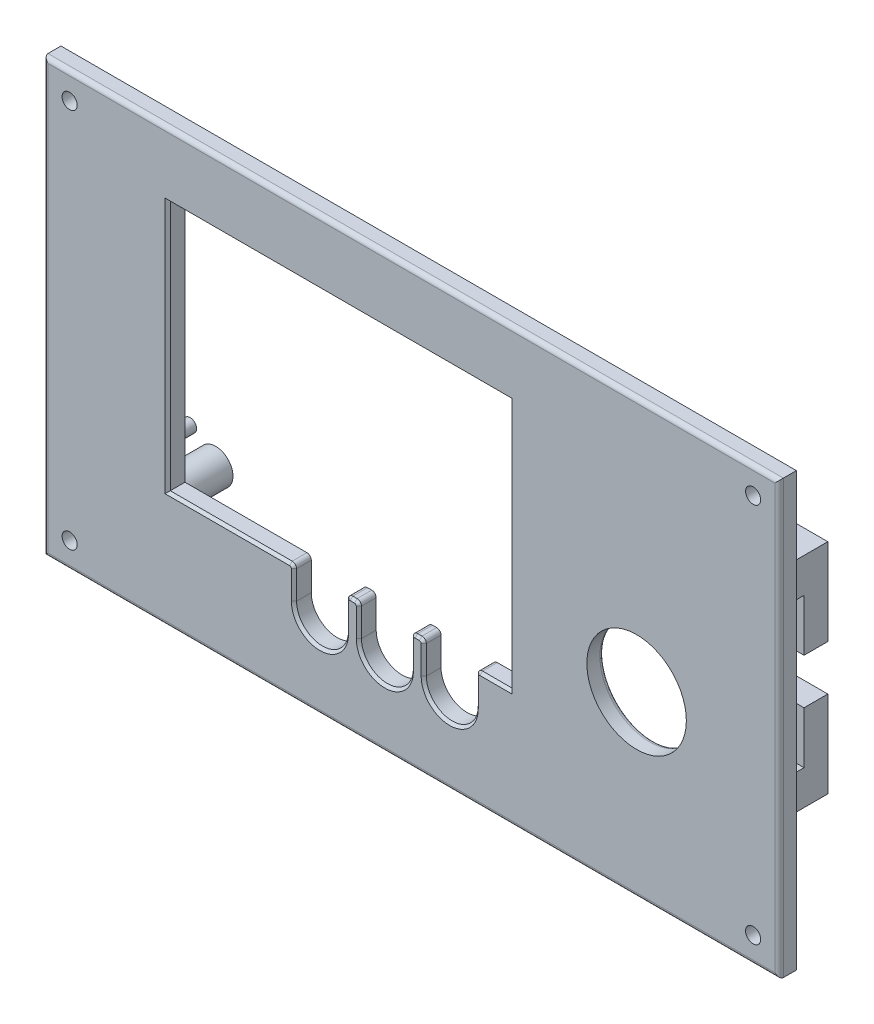
SolidWorks part; units mm, degrees
ref_plane "前视基准面" through (0, 0, 0) normal (0, 0, 1) x (1, 0, 0)
ref_plane "上视基准面" through (0, 0, 0) normal (0, 1, 0) x (1, 0, 0)
ref_plane "右视基准面" through (0, 0, 0) normal (1, 0, 0) x (0, 0, -1)
sketch "草图1" plane through (0, 0, 0) normal (0, 0, 1) x (1, 0, 0)
  line L0 (-37.3122, -36.0521) -> (-37.3122, -29.5521)
  line L1 (-95.1737, 44.4479) -> (74.8263, 44.4479)
  line L2 (-95.1737, 44.4479) -> (-95.1737, -55.5521)
  line L3 (-95.1737, -55.5521) -> (74.8263, -55.5521)
  line L4 (74.8263, 44.4479) -> (74.8263, -55.5521)
  line L5 (-66.5122, 29.4479) -> (12.4878, 29.4479)
  line L6 (-66.5122, 29.4479) -> (-66.5122, -28.5521)
  line L7 (-66.5122, -28.5521) -> (-38.3122, -28.5521)
  line L8 (12.4878, 29.4479) -> (12.4878, -28.5521)
  line L9 (-25.3122, -36.0521) -> (-25.3122, -29.5521)
  line L10 (-22.3122, -36.0521) -> (-22.3122, -29.5521)
  line L11 (-10.3122, -36.0521) -> (-10.3122, -29.5521)
  line L12 (4.6878, -36.0521) -> (4.6878, -29.5521)
  line L13 (-7.3122, -36.0521) -> (-7.3122, -29.5521)
  line L14 (-9.3122, -28.5521) -> (-8.3122, -28.5521)
  line L15 (-24.3122, -28.5521) -> (-23.3122, -28.5521)
  line L16 (5.6878, -28.5521) -> (12.4878, -28.5521)
  line L17 (-124.387, -5.5521) -> (115.7524, -5.5521) construction
  line L18 (-10.1737, 93.3642) -> (-10.1737, -86.2543) construction
  circle A0 centre (41.8878, -14.3521) radius 11.5
  arc A1 (-37.3122, -36.0521) -> (-25.3122, -36.0521) centre (-31.3122, -36.0521) ccw
  arc A2 (-22.3122, -36.0521) -> (-10.3122, -36.0521) centre (-16.3122, -36.0521) ccw
  arc A3 (-7.3122, -36.0521) -> (4.6878, -36.0521) centre (-1.3122, -36.0521) ccw
  arc A4 (4.6878, -29.5521) -> (5.6878, -28.5521) centre (5.6878, -29.5521) cw
  arc A5 (-7.3122, -29.5521) -> (-8.3122, -28.5521) centre (-8.3122, -29.5521) ccw
  arc A6 (-10.3122, -29.5521) -> (-9.3122, -28.5521) centre (-9.3122, -29.5521) cw
  arc A7 (-22.3122, -29.5521) -> (-23.3122, -28.5521) centre (-23.3122, -29.5521) ccw
  arc A8 (-25.3122, -29.5521) -> (-24.3122, -28.5521) centre (-24.3122, -29.5521) cw
  arc A9 (-37.3122, -29.5521) -> (-38.3122, -28.5521) centre (-38.3122, -29.5521) ccw
  circle A10 centre (-89.1737, 38.4479) radius 1.75
  circle A11 centre (68.8263, 38.4479) radius 1.75
  circle A12 centre (68.8263, -49.5521) radius 1.75
  circle A13 centre (-89.1737, -49.5521) radius 1.75
  point P15 (4.6878, -28.5521)
  point P30 (-7.3122, -28.5521)
  point P33 (-10.3122, -28.5521)
  point P38 (-25.3122, -28.5521)
  point P49 (0, 0)
  dimension "D7" = 23
  dimension "D9" = 12
  dimension "D10" = 15
  dimension "D11" = 15
  dimension "D12" = 13.8
  dimension "D13" = 7.5
  dimension "D14" = 1
  dimension "D15" = 3.5
  dimension "D16" = 6
  dimension "D1" = 170
  dimension "D2" = 100
  dimension "D3" = 58
  dimension "D4" = 79
  dimension "D5" = 29.4
  dimension "D6" = 14.2
  dimension "D8" = 15
  dimension "D17" = 6
extrude "凸台-拉伸1" add sketch "草图1" along normal blind 4
chamfer "倒角1" distance 0.6 angle 45 22 edges at (-37.6051, -28.845, 4) (-37.3122, -32.8021, 4) (-31.3122, -42.0521, 4) (-25.3122, -32.8021, 4) (-25.0193, -28.845, 4) (-23.8122, -28.5521, 4) (-22.6051, -28.845, 4) (-22.3122, -32.8021, 4) (-16.3122, -42.0521, 4) (-10.3122, -32.8021, 4) (-10.0193, -28.845, 4) (-8.8122, -28.5521, 4) (-7.6051, -28.845, 4) (-7.3122, -32.8021, 4) (-1.3122, -42.0521, 4) (4.6878, -32.8021, 4) (4.9807, -28.845, 4) (9.0878, -28.5521, 4) (-52.4122, -28.5521, 4) (12.4878, 0.4479, 4) (-27.0122, 29.4479, 4) (-66.5122, 0.4479, 4)
fillet "圆角1" radius 1 1 edges at (53.3878, -14.3521, 0)
sketch "草图2" plane through (0, 0, 0) normal (0, 0, -1) x (-1, 0, 0)
  line L0 (-66.1828, 0.4479) -> (115.6018, 0.4479) construction
  line L1 (-12.4878, 29.4479) -> (66.5122, 29.4479) construction
  line L2 (66.5122, -28.5521) -> (38.3122, -28.5521) construction
  line L3 (66.5122, 29.4479) -> (66.5122, -28.5521) construction
  line L4 (-17.9878, 25.3979) -> (73.3122, 25.3979) construction
  line L5 (-10.6878, -37.8021) -> (75.4122, -37.8021) construction
  circle A0 centre (-17.9878, 25.3979) radius 1.5
  circle A2 centre (73.3122, 25.3979) radius 1.5
  circle A3 centre (73.3122, -24.5021) radius 1.5
  circle A4 centre (-17.9878, -24.5021) radius 1.5
  circle A5 centre (75.4122, -37.8021) radius 4
  circle A6 centre (75.4122, -37.8021) radius 1.5
  circle A7 centre (-10.6878, -37.8021) radius 4
  arc A8 (-4.6878, -36.0521) -> (7.3122, -36.0521) centre (1.3122, -36.0521) ccw construction
  circle A9 centre (-10.6878, -37.8021) radius 1.5
  dimension "D1" = 91.3
  dimension "D2" = 6.8
  dimension "D3" = 3
  dimension "D4" = 13.3
  dimension "D5" = 2.1
  dimension "D6" = 8
  dimension "D7" = 3
  dimension "D8" = 12
  dimension "D9" = 8
  dimension "D10" = 3
  dimension "D11" = 49.9
extrude "凸台-拉伸2" add sketch "草图2" along normal blind 16
fillet "圆角2" radius 1 4 edges at (74.8263, -5.5521, 4) (-10.1737, 44.4479, 4) (-10.1737, -55.5521, 4) (-95.1737, -5.5521, 4)
sketch "草图3" plane through (0, 0, 0) normal (1, 0, 0) x (0, 0, -1)
  line L0 (0, -55.5521) -> (0, 44.4479) construction
  line L1 (8, 34.7762) -> (20.6651, 34.7762)
  line L2 (8, 34.7762) -> (8, -29.2158)
  line L3 (8, -29.2158) -> (20.6651, -29.2158)
  line L4 (20.6651, 34.7762) -> (20.6651, -29.2158)
  dimension "D1" = 8
extrude "切除-拉伸1" cut sketch "草图3" against normal mid plane 170
sketch "草图4" plane through (0, 0, 0) normal (0, 0, -1) x (-1, 0, 0)
  line L0 (-84.5714, -14.3521) -> (0, -14.3521) construction
  line L1 (-41.8878, 16.0764) -> (-41.8878, -50.4729) construction
  line L2 (-58.9378, -0.4521) -> (-58.9378, -26.4521) construction
  line L3 (-58.9378, -0.4521) -> (-24.8378, -0.4521) construction
  line L4 (-24.8378, -0.4521) -> (-24.8378, -26.4521) construction
  line L5 (-24.8378, -26.4521) -> (-58.9378, -26.4521) construction
  line L6 (-55.0878, -11.0719) -> (-55.0878, 15.8519) construction
  line L7 (-60.0878, 11.8479) -> (-50.0878, 11.8479)
  line L8 (-60.0878, 11.8479) -> (-60.0878, -8.1521)
  line L9 (-60.0878, -8.1521) -> (-50.0878, -8.1521)
  line L10 (-50.0878, 11.8479) -> (-50.0878, -8.1521)
  line L11 (-23.6878, -8.1521) -> (-33.6878, -8.1521)
  line L12 (-23.6878, 11.8479) -> (-33.6878, 11.8479)
  line L13 (-33.6878, 11.8479) -> (-33.6878, -8.1521)
  line L14 (-23.6878, 11.8479) -> (-23.6878, -8.1521)
  line L15 (-55.0878, -18.9352) -> (-55.0878, -43.9665) construction
  line L17 (-60.0878, -18.6521) -> (-50.0878, -18.6521)
  line L18 (-60.0878, -18.6521) -> (-60.0878, -38.6521)
  line L19 (-60.0878, -38.6521) -> (-50.0878, -38.6521)
  line L20 (-50.0878, -18.6521) -> (-50.0878, -38.6521)
  circle A0 centre (-28.6878, -3.1521) radius 1.5 construction
  circle A1 centre (-55.0878, -3.1521) radius 1.5 construction
  circle A2 centre (-28.6878, -23.6521) radius 1.5 construction
  circle A3 centre (-55.0878, -23.6521) radius 1.5 construction
  circle A4 centre (-55.0878, -3.1521) radius 1.5
  circle A5 centre (-28.6878, -3.1521) radius 1.5
  circle A6 centre (-55.0878, -23.6521) radius 1.5
  point P23 (-55.0878, -8.1521)
  dimension "D1" = 26.4
  dimension "D2" = 20.5
  dimension "D5" = 3
  dimension "D6" = 11.2
  dimension "D7" = 20.5
  dimension "D9" = 10
  dimension "D3" = 26
  dimension "D4" = 34.1
  dimension "D8" = 13.9
  dimension "D10" = 20
  dimension "D11" = 5
  dimension "D12" = 10
  dimension "D13" = 20
  dimension "D14" = 5
extrude "凸台-拉伸3" add sketch "草图4" along normal blind 22
sketch "草图5" plane through (60.0878, 0, 0) normal (1, 0, 0) x (0, 0, -1)
  line L0 (0, 11.8479) -> (0, -8.1521) construction
  line L1 (0, 3.8479) -> (16.5, 3.8479)
  line L2 (0, 3.8479) -> (0, -30.6521)
  line L3 (0, -30.6521) -> (16.5, -30.6521)
  line L4 (16.5, 3.8479) -> (16.5, -30.6521)
  line L5 (22, 11.8479) -> (0, 11.8479) construction
  line L6 (22, -38.6521) -> (0, -38.6521) construction
  line L7 (22, 11.8479) -> (22, -8.1521) construction
  dimension "D1" = 8
  dimension "D2" = 8
  dimension "D3" = 5.5
extrude "切除-拉伸2" cut sketch "草图5" against normal blind 39
fillet "圆角3" radius 2 12 edges at (55.0878, -30.6521, 0) (50.0878, -34.6521, 0) (55.0878, -38.6521, 0) (60.0878, -34.6521, 0) (55.0878, 3.8479, 0) (50.0878, 7.8479, 0) (60.0878, 7.8479, 0) (55.0878, 11.8479, 0) (33.6878, 7.8479, 0) (28.6878, 11.8479, 0) (23.6878, 7.8479, 0) (28.6878, 3.8479, 0)
fillet "圆角4" radius 1 5 edges at (-71.8122, -24.5021, 0) (-71.8122, 25.3979, 0) (19.4878, 25.3979, 0) (19.4878, -24.5021, 0) (14.6878, -37.8021, 0)
